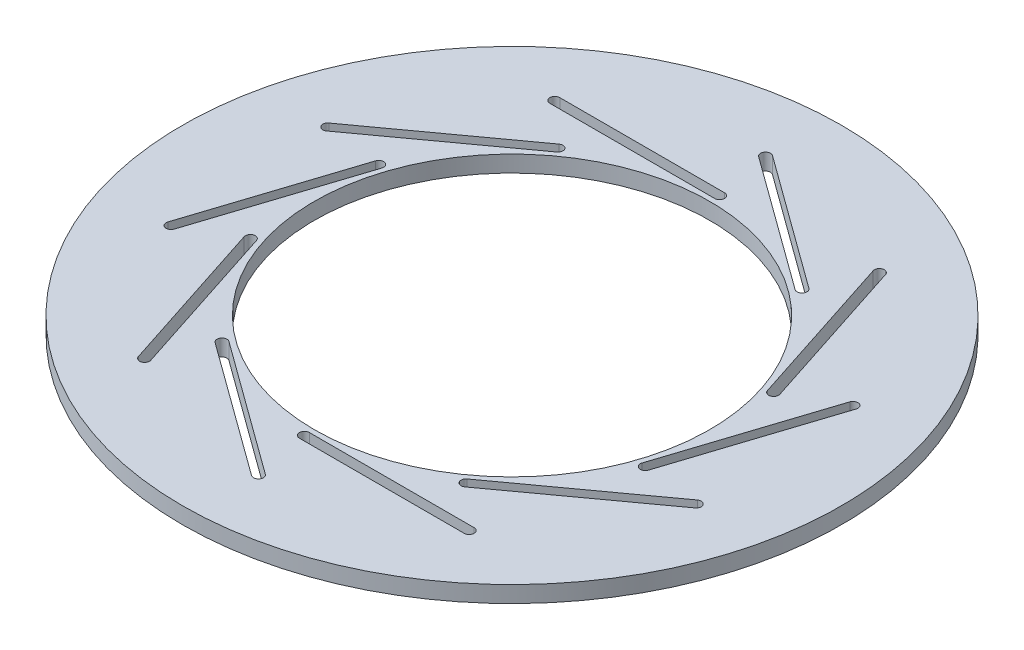
SolidWorks part; units mm, degrees
ref_plane "Front Plane" through (0, 0, 0) normal (0, 0, 1) x (1, 0, 0)
ref_plane "Top Plane" through (0, 0, 0) normal (0, 1, 0) x (1, 0, 0)
ref_plane "Right Plane" through (0, 0, 0) normal (1, 0, 0) x (0, 0, -1)
sketch "Sketch1" plane through (0, 0, 0) normal (0, 1, 0) x (1, 0, 0)
  line L0 (0, -100) -> (0, 100) construction
  line L1 (-100, 0) -> (100, 0) construction
  line L2 (0, 63) -> (-50, 63) construction
  line L3 (0, 61.5) -> (-50, 61.5)
  line L4 (0, 64.5) -> (-50, 64.5)
  line L5 (37.0305, 50.9681) -> (-3.4204, 80.3573) construction
  line L6 (36.1488, 49.7545) -> (-4.3021, 79.1438)
  line L7 (37.9121, 52.1816) -> (-2.5387, 81.5709)
  line L8 (59.9166, 19.4681) -> (44.4657, 67.0209) construction
  line L9 (58.49, 19.0045) -> (43.0391, 66.5574)
  line L10 (61.3431, 19.9316) -> (45.8923, 67.4844)
  line L11 (59.9166, -19.4681) -> (75.3674, 28.0848) construction
  line L12 (58.49, -19.0045) -> (73.9408, 28.5483)
  line L13 (61.3431, -19.9316) -> (76.794, 27.6212)
  line L14 (37.0305, -50.9681) -> (77.4813, -21.5788) construction
  line L15 (36.1488, -49.7545) -> (76.5996, -20.3653)
  line L16 (37.9121, -52.1816) -> (78.363, -22.7923)
  line L17 (0, -63) -> (50, -63) construction
  line L18 (0, -61.5) -> (50, -61.5)
  line L19 (0, -64.5) -> (50, -64.5)
  line L20 (-37.0305, -50.9681) -> (3.4204, -80.3573) construction
  line L21 (-36.1488, -49.7545) -> (4.3021, -79.1438)
  line L22 (-37.9121, -52.1816) -> (2.5387, -81.5709)
  line L23 (-59.9166, -19.4681) -> (-44.4657, -67.0209) construction
  line L24 (-58.49, -19.0045) -> (-43.0391, -66.5574)
  line L25 (-61.3431, -19.9316) -> (-45.8923, -67.4844)
  line L26 (-59.9166, 19.4681) -> (-75.3674, -28.0848) construction
  line L27 (-58.49, 19.0045) -> (-73.9408, -28.5483)
  line L28 (-61.3431, 19.9316) -> (-76.794, -27.6212)
  line L29 (-37.0305, 50.9681) -> (-77.4813, 21.5788) construction
  line L30 (-36.1488, 49.7545) -> (-76.5996, 20.3653)
  line L31 (-37.9121, 52.1816) -> (-78.363, 22.7923)
  circle A0 centre (0, 0) radius 60
  circle A1 centre (0, 0) radius 100
  circle A2 centre (0, 0) radius 63 construction
  arc A3 (0, 61.5) -> (0, 64.5) centre (0, 63) ccw
  arc A4 (-50, 64.5) -> (-50, 61.5) centre (-50, 63) ccw
  arc A5 (36.1488, 49.7545) -> (37.9121, 52.1816) centre (37.0305, 50.9681) ccw
  arc A6 (-2.5387, 81.5709) -> (-4.3021, 79.1438) centre (-3.4204, 80.3573) ccw
  arc A7 (58.49, 19.0045) -> (61.3431, 19.9316) centre (59.9166, 19.4681) ccw
  arc A8 (45.8923, 67.4844) -> (43.0391, 66.5574) centre (44.4657, 67.0209) ccw
  arc A9 (58.49, -19.0045) -> (61.3431, -19.9316) centre (59.9166, -19.4681) ccw
  arc A10 (76.794, 27.6212) -> (73.9408, 28.5483) centre (75.3674, 28.0848) ccw
  arc A11 (36.1488, -49.7545) -> (37.9121, -52.1816) centre (37.0305, -50.9681) ccw
  arc A12 (78.363, -22.7923) -> (76.5996, -20.3653) centre (77.4813, -21.5788) ccw
  arc A13 (0, -61.5) -> (0, -64.5) centre (0, -63) ccw
  arc A14 (50, -64.5) -> (50, -61.5) centre (50, -63) ccw
  arc A15 (-36.1488, -49.7545) -> (-37.9121, -52.1816) centre (-37.0305, -50.9681) ccw
  arc A16 (2.5387, -81.5709) -> (4.3021, -79.1438) centre (3.4204, -80.3573) ccw
  arc A17 (-58.49, -19.0045) -> (-61.3431, -19.9316) centre (-59.9166, -19.4681) ccw
  arc A18 (-45.8923, -67.4844) -> (-43.0391, -66.5574) centre (-44.4657, -67.0209) ccw
  arc A19 (-58.49, 19.0045) -> (-61.3431, 19.9316) centre (-59.9166, 19.4681) ccw
  arc A20 (-76.794, -27.6212) -> (-73.9408, -28.5483) centre (-75.3674, -28.0848) ccw
  arc A21 (-36.1488, 49.7545) -> (-37.9121, 52.1816) centre (-37.0305, 50.9681) ccw
  arc A22 (-78.363, 22.7923) -> (-76.5996, 20.3653) centre (-77.4813, 21.5788) ccw
  point P11 (-25, 63)
  point P21 (16.805, 65.6627)
  point P28 (52.1911, 43.2445)
  point P35 (67.642, 4.3083)
  point P42 (57.2559, -36.2734)
  point P49 (25, -63)
  point P56 (-16.805, -65.6627)
  point P63 (-52.1911, -43.2445)
  point P70 (-67.642, -4.3083)
  point P77 (-57.2559, 36.2734)
  point P82 (0, 0)
  dimension "D1" = 120
  dimension "D2" = 200
  dimension "D3" = 126
  dimension "D4" = 1.5
  dimension "D5" = 50
  dimension "D6" = 10
extrude "Boss-Extrude1" add sketch "Sketch1" along normal blind 5
